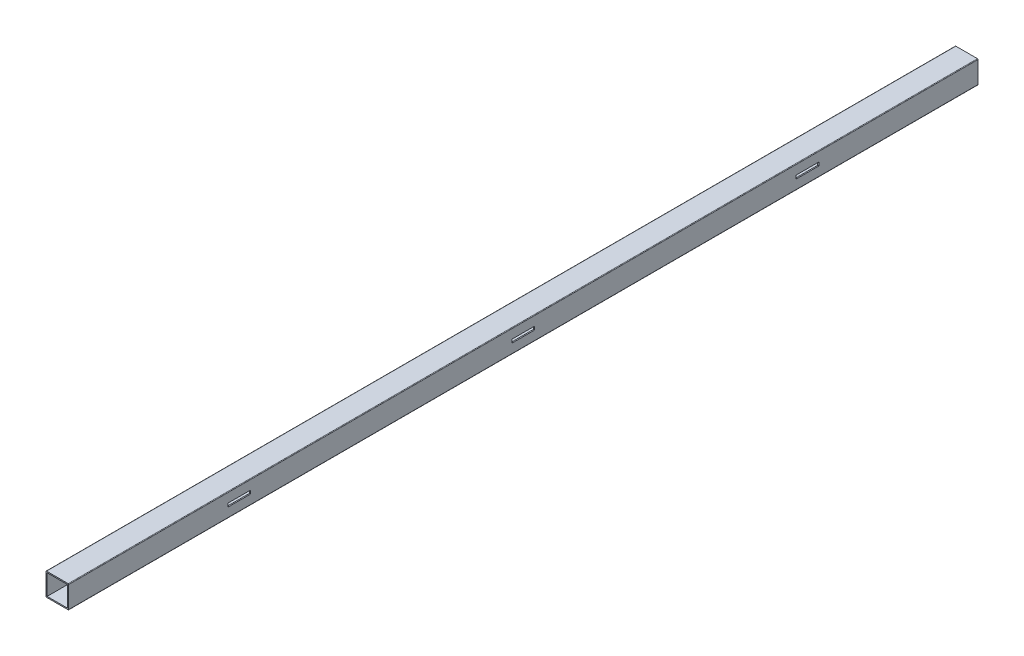
SolidWorks part; units mm, degrees
material "St.37"
ref_plane "Front Plane" through (0, 0, 0) normal (0, 0, 1) x (1, 0, 0)
ref_plane "Top Plane" through (0, 0, 0) normal (0, 1, 0) x (1, 0, 0)
ref_plane "Right Plane" through (0, 0, 0) normal (1, 0, 0) x (0, 0, -1)
sketch "Sketch1" plane through (0, 0, 0) normal (0, 0, 1) x (1, 0, 0)
  line L1 (-9.5, -10) -> (9.5, -10)
  line L2 (-10, -9.5) -> (-10, 9.5)
  line L3 (-9.5, 10) -> (9.5, 10)
  line L4 (10, -9.5) -> (10, 9.5)
  line L5 (-10, -10) -> (10, 10) construction
  line L6 (-10, 10) -> (10, -10) construction
  arc A0 (-9.5, -10) -> (-10, -9.5) centre (-9.5, -9.5) cw
  arc A1 (9.5, -10) -> (10, -9.5) centre (9.5, -9.5) ccw
  arc A2 (9.5, 10) -> (10, 9.5) centre (9.5, 9.5) cw
  arc A3 (-10, 9.5) -> (-9.5, 10) centre (-9.5, 9.5) cw
  point P0 (0, 0)
  dimension "D3" = 0.5
  dimension "D1" = 20
  dimension "D2" = 20
extrude "Extrude-Thin1" add sketch "Sketch1" along normal blind 800 thin
sketch "Sketch2" plane through (10, 0, 0) normal (1, 0, 0) x (0, 0, -1)
  line L0 (0, -9.5) -> (0, 9.5) construction
  line L1 (-140, -1.5) -> (-160, -1.5)
  line L2 (-140, -1.5) -> (-140, 1.5)
  line L3 (-140, 1.5) -> (-160, 1.5)
  line L4 (-160, -1.5) -> (-160, 1.5)
  line L5 (-140, -1.5) -> (-160, 1.5) construction
  line L6 (-140, 1.5) -> (-160, -1.5) construction
  line L7 (-800, -10) -> (0, -10) construction
  line L8 (-390, -1.5) -> (-390, 1.5)
  line L9 (-390, -1.5) -> (-410, -1.5)
  line L10 (-410, -1.5) -> (-410, 1.5)
  line L11 (-390, 1.5) -> (-410, 1.5)
  line L12 (-640, -1.5) -> (-640, 1.5)
  line L13 (-640, -1.5) -> (-660, -1.5)
  line L14 (-660, -1.5) -> (-660, 1.5)
  line L15 (-640, 1.5) -> (-660, 1.5)
  line L16 (-800, -9.5) -> (-800, 9.5) construction
  point P0 (-150, 0)
  dimension "D1" = 140
  dimension "D2" = 3
  dimension "D3" = 10
  dimension "D4" = 20
  dimension "D6" = 140
  dimension "D5" = 3
extrude "Cut-Extrude1" cut sketch "Sketch2" against normal blind 10
sketch "Sketch3" plane through (0, -10, 0) normal (0, -1, 0) x (1, 0, 0)
  line L0 (-9.5, 0) -> (9.5, 0) construction
  line L1 (-9.5, 800) -> (9.5, 800) construction
  circle A0 centre (0, 25) radius 2.5
  circle A1 centre (0, 275) radius 2.5
  circle A2 centre (0, 525) radius 2.5
  circle A3 centre (0, 775) radius 2.5
  point P13 (0, 0)
  dimension "D1" = 25
  dimension "D2" = 5
  dimension "D4" = 25
  dimension "D3" = 4
extrude "Cut-Extrude2" cut sketch "Sketch3" against normal blind 10
